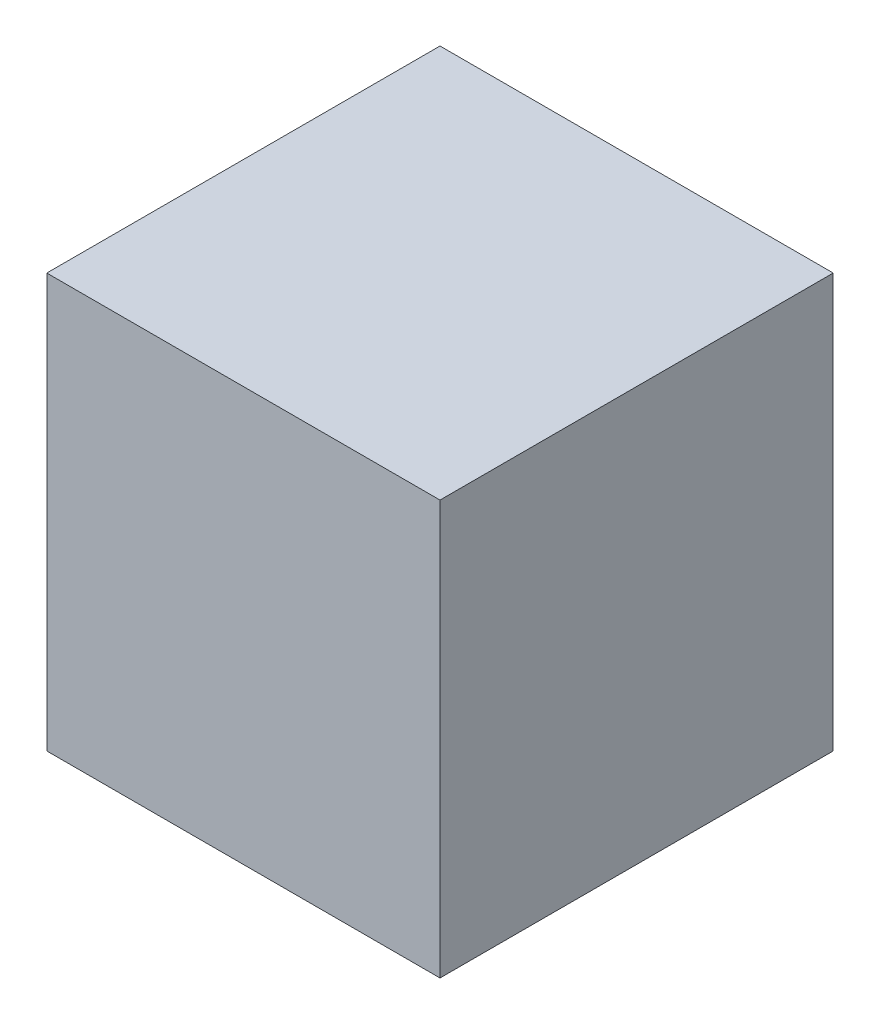
SolidWorks part; units mm, degrees
ref_plane "Front Plane" through (0, 0, 0) normal (0, 0, 1) x (1, 0, 0)
ref_plane "Top Plane" through (0, 0, 0) normal (0, 1, 0) x (1, 0, 0)
ref_plane "Right Plane" through (0, 0, 0) normal (1, 0, 0) x (0, 0, -1)
sketch "Sketch1" plane through (0, 0, 0) normal (0, 1, 0) x (1, 0, 0)
  line L1 (241.3, -241.3) -> (-241.3, -241.3)
  line L2 (241.3, -241.3) -> (241.3, 241.3)
  line L3 (241.3, 241.3) -> (-241.3, 241.3)
  line L4 (-241.3, -241.3) -> (-241.3, 241.3)
  line L5 (241.3, -241.3) -> (-241.3, 241.3) construction
  line L6 (241.3, 241.3) -> (-241.3, -241.3) construction
  point P0 (0, 0)
  dimension "D1" = 482.6
  dimension "D2" = 482.6
extrude "Boss-Extrude1" add sketch "Sketch1" along normal blind 508
